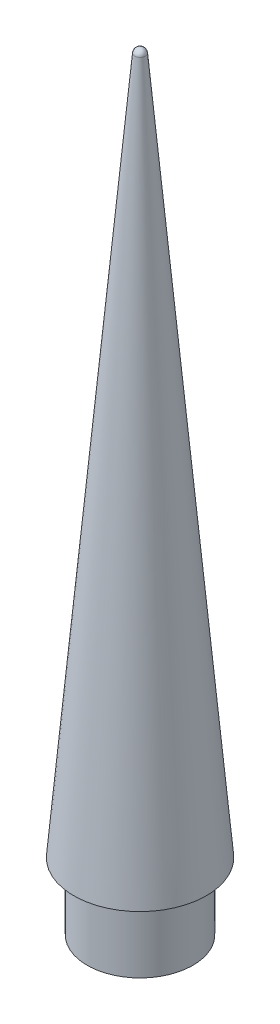
SolidWorks part; units mm, degrees
ref_plane "Front Plane" through (0, 0, 0) normal (0, 0, 1) x (1, 0, 0)
ref_plane "Top Plane" through (0, 0, 0) normal (0, 1, 0) x (1, 0, 0)
ref_plane "Right Plane" through (0, 0, 0) normal (1, 0, 0) x (0, 0, -1)
sketch "Sketch1" plane through (0, 0, 0) normal (0, 0, 1) x (1, 0, 0)
  line L0 (0, 0) -> (0, 133.0688)
  line L1 (1.0121, 132.1413) -> (12.573, 0)
  line L2 (12.573, 0) -> (0, 0)
  arc A0 (1.0121, 132.1413) -> (0, 133.0688) centre (0, 132.0528) ccw
  dimension "D3" = 1.016
  dimension "D1" = 5
  dimension "D2" = 12.573
revolve "Revolve2" add sketch "Sketch1" angle 360 about L0
sketch "Sketch2" plane through (0, 0, 0) normal (0, -1, 0) x (1, 0, 0)
  circle A0 centre (0, 0) radius 10.033
  dimension "D1" = 20.066
extrude "Boss-Extrude1" add sketch "Sketch2" along normal blind 12.7
sketch "Sketch3" plane through (0, -12.7, 0) normal (0, -1, 0) x (1, 0, 0)
  point P0 (0, 0)
hole_wizard "M3x0.5 Tapped Hole1" positions "Sketch3" profile "Sketch4" tap size "M3x0.5" standard "ANSI Metric"
sketch "Sketch4" plane through (0, -12.7, 0) normal (1, 0, 0) x (0, 0, -1)
  line L0 (0, 0) -> (0, 10.9111)
  line L1 (0, 10.9111) -> (1.25, 10.16)
  line L2 (1.25, 10.16) -> (1.25, 0)
  line L5 (1.25, 0) -> (0, 0)
  line L10 (0, 10.9111) -> (-1.25, 10.16) construction
  line L11 (0, -6.35) -> (0, 107.95) construction
  dimension "Tap Drill Dia." = 2.5
  dimension "Tap Drill Depth" = 10.16
  dimension "Drill Angle" = 118
cosmetic thread "Hole Thread1" parameters "D1"=7.62, "D2"=3
